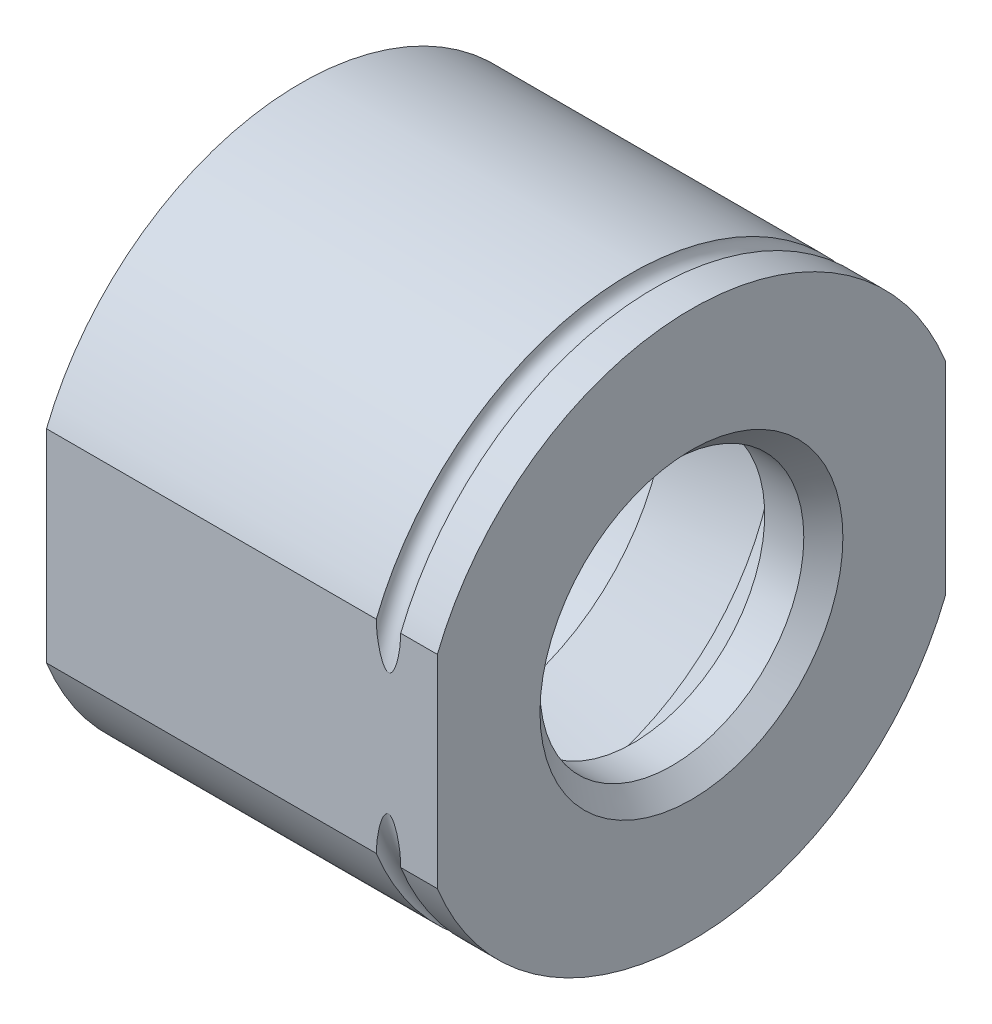
SolidWorks part; units mm, degrees
ref_plane "Front" through (0, 0, 0) normal (0, 0, 1) x (1, 0, 0)
ref_plane "Top" through (0, 0, 0) normal (0, 1, 0) x (1, 0, 0)
ref_plane "Right" through (0, 0, 0) normal (1, 0, 0) x (0, 0, -1)
ref_plane "Plane1" through (1.9304, 0, 0) normal (1, 0, 0) x (0, 0, -1)
sketch "Sketch1" plane through (1.9304, 0, 0) normal (1, 0, 0) x (0, 0, -1)
  line L0 (1.3208, -0.5273) -> (1.3208, 0.5273)
  line L1 (-1.3208, 0.5273) -> (-1.3208, -0.5273)
  line L2 (0, 0) -> (0, 3.338) construction
  arc A0 (1.3208, 0.5273) -> (-1.3208, 0.5273) centre (0, 0) ccw
  arc A1 (-1.3208, -0.5273) -> (1.3208, -0.5273) centre (0, 0) ccw
  dimension "D1" = 1.4222
  dimension "D2" = 1.4222
  dimension "D3" = 1.3208
extrude "Boss-Extrude1" add sketch "Sketch1" against normal blind 2.032
ref_plane "Plane2" through (0, 0, 0) normal (0, 0, -1) x (-1, 0, 0)
sketch "Sketch2" plane through (0, 0, 0) normal (0, 0, -1) x (-1, 0, 0)
  line L0 (-1.9304, 0.6858) -> (-1.9304, 0)
  line L1 (-1.9304, 0) -> (0.1016, 0)
  line L2 (0.1016, 0) -> (0.1016, 1.1049)
  line L3 (0.1016, 1.1049) -> (-0.8128, 1.1049)
  line L4 (-0.8128, 1.1049) -> (-0.8128, 0.9874)
  line L5 (-0.8128, 0.9874) -> (-1.2192, 1.1557)
  line L6 (-1.2192, 1.1557) -> (-1.6256, 0.9874)
  line L7 (-1.6256, 0.9874) -> (-1.6256, 0.6858)
  line L8 (-1.6256, 0.6858) -> (-1.9304, 0.6858)
  line L9 (-1.9304, 0) -> (0.1016, 0) construction
  dimension "D1" = 0.3048
  dimension "D2" = 0.7112
  dimension "D3" = 1.1176
  dimension "D4" = 2.032
  dimension "D5" = 0.6858
  dimension "D6" = 0.9874
  dimension "D7" = 1.1049
  dimension "D8" = 1.1557
revolve "Cut-Revolve1" cut sketch "Sketch2" angle 360 about L9
chamfer "Chamfer1" distance 0.1016 angle 45 1 edges at (1.9304, 0, 0.6858)
sketch "Sketch3" plane through (0, 0, 0) normal (0, 0, 1) x (1, 0, 0)
  line L1 (1.7399, 1.4222) -> (1.6129, 1.4222)
  line L3 (1.9304, 1.4222) -> (-0.1016, 1.4222) construction
  line L4 (1.9304, -2.0872) -> (1.9304, 2.0872) construction
  arc A1 (1.6129, 1.4222) -> (1.7399, 1.4222) centre (1.6764, 1.4222) ccw
  dimension "D2" = 0.254
  dimension "D1" = 0.0635
revolve "Cut-Revolve2" cut sketch "Sketch3" angle 360 about axis through (-0.1016, 0, 0) along (1, 0, 0)
